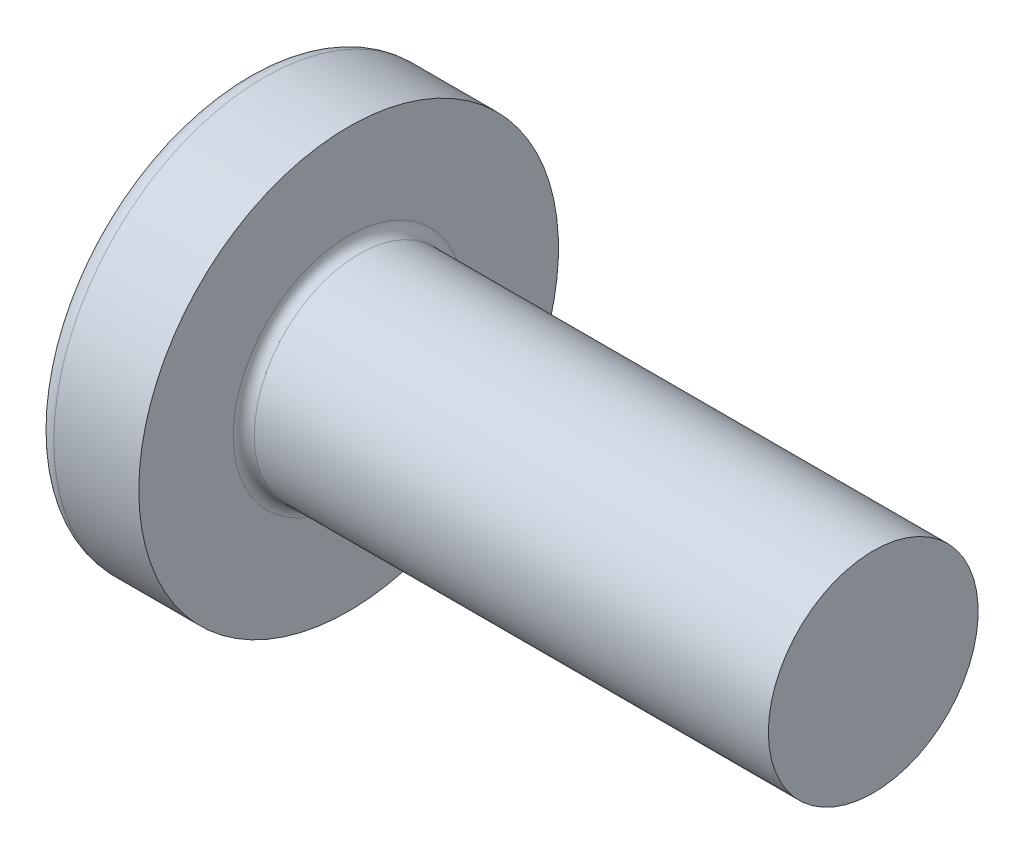
SolidWorks part; units mm, degrees
material "2018 合金"
ref_plane "Plane1" through (0, 0, 0) normal (0, 0, 1) x (1, 0, 0)
ref_plane "Plane2" through (0, 0, 0) normal (0, 1, 0) x (1, 0, 0)
ref_plane "Plane3" through (0, 0, 0) normal (1, 0, 0) x (0, 0, -1)
sketch "BodySke" plane through (0, 0, 0) normal (0, 0, 1) x (1, 0, 0)
  line L0 (1.6, 1) -> (1.6, 2)
  line L1 (1.8, 6.35) -> (1.8, -3.175) construction
  line L2 (-25.4, 0) -> (127, 0) construction
  line L3 (6.6, 0) -> (0, 0)
  line L4 (1.6, 1) -> (6.6, 1)
  line L5 (6.6, 1) -> (6.6, 0)
  line L6 (0.79, 2) -> (1.6, 2)
  line L8 (1.6, 6.35) -> (1.6, -3.175) construction
  arc A0 (0.6464, 1.9285) -> (0, 0) centre (3.2, 0) ccw
  arc A2 (0.6464, 1.9285) -> (0.79, 2) centre (0.79, 1.82) cw
  dimension "Head_crown_rad" = 3.2
  dimension "Head_fillet_rad" = 0.18
  dimension "Length" = 5
  dimension "Head_ht" = 1.6
  dimension "Head_dia" = 4
  dimension "Advance" = 0.4
  dimension "Thread_nom" = 5
  dimension "Diameter" = 2
revolve "Base-Revolve" add sketch "BodySke"
cosmetic thread "ThreadCosmetic" [suppressed]
fillet "Fillet1" radius 0.1 1 edges at (1.6, 0, 1)
sketch "Sketch3" plane through (0, 0, 0) normal (1, 0, 0) x (0, 0, -1)
  line L0 (0.24, -1.05) -> (-0.24, -1.05)
  line L1 (0.24, -1.05) -> (0.24, 1.05)
  line L2 (-0.24, 1.05) -> (0.24, 1.05)
  line L3 (-0.24, 1.05) -> (-0.24, -1.05)
  dimension "Cross_dia" = 2.1
  dimension "D1" = 1.05
  dimension "Cross_width" = 0.48
  dimension "D2" = 0.24
ref_plane "Plane4" through (1.42, 0, 0) normal (1, 0, 0) x (0, 0, -1)
sketch "Sketch4" plane through (1.42, 0, 0) normal (1, 0, 0) x (0, 0, -1)
  line L0 (0.24, -0.342) -> (-0.24, -0.342)
  line L1 (0.24, -0.342) -> (0.24, 0.342)
  line L2 (-0.24, 0.342) -> (0.24, 0.342)
  line L3 (-0.24, 0.342) -> (-0.24, -0.342)
  dimension "D1" = 0.48
  dimension "D2" = 0.684
  dimension "D3" = 0.24
  dimension "D4" = 0.342
loft "Recess" cut profiles "Sketch3", "Sketch4"
pattern_circular "RecPat" count 2 every 90 about axis through (0, 0, 0) along (1, 0, 0) of "Recess"
sketch "RecCorSke" plane through (0, 0, 0) normal (0, 0, 1) x (1, 0, 0)
  line L0 (-3.175, 0) -> (15.875, 0) construction
  line L1 (-25.4, 0) -> (127, 0) construction
  line L2 (0, 0) -> (0, 0.4548)
  line L3 (0, 0.4548) -> (1.42, 0.3555)
  line L4 (1.42, 0.3555) -> (1.5355, 0)
  line L5 (1.5355, 0) -> (0, 0)
  dimension "Diameter" = 0.711
  dimension "Depth" = 1.42
  dimension "Draft_angle" = 4
  dimension "Bottom_angle" = 18
revolve "RecessCore" cut sketch "RecCorSke" angle 360 about L0
sketch "ThdSchSke" plane through (0, 0, 0) normal (0, 0, 1) x (1, 0, 0)
  line L0 (2.4, -0.774) -> (2.2418, -1)
  line L1 (2.4, -0.774) -> (2.5582, -1)
  line L2 (2.5582, -1) -> (2.5582, -1.25)
  line L3 (-3.175, 0) -> (5.1513, 0) construction
  line L5 (2.5582, -1.25) -> (2.2418, -1.25)
  line L6 (2.2418, -1.25) -> (2.2418, -1)
  dimension "Diameter" = 2
  dimension "SideAngle" = 55
  dimension "VeeAngle" = 70
  dimension "Thread_minor" = 1.548
  dimension "Overcut" = 2.5
  dimension "Start" = 2.4
revolve "ThreadSchematic" [suppressed] cut sketch "ThdSchSke" angle 360 about L3
pattern_linear "ThdSchPat" [suppressed]
equation "\"D1@Sketch3\" = \"Cross_dia@Sketch3\" / 2"
equation "\"D2@Sketch3\" = \"Cross_width@Sketch3\" / 2"
equation "\"Depth@RecCorSke\" = \"Cross_depth@Plane4\""
equation "\"D1@Sketch4\" = \"Cross_width@Sketch3\""
equation "\"D2@Sketch4\" = \"Cross_dia@Sketch3\" - 2.0 * \"Cross_depth@Plane4\" * tan(26.5  * 0.017453292)"
equation "\"D3@Sketch4\" = \"D1@Sketch4\" / 2"
equation "\"D4@Sketch4\" = \"D2@Sketch4\" / 2"
equation "\"Thread_length@ThreadCosmetic\" = ((sgn( (\"Length@BodySke\" - \"Advance@BodySke\" * 2.0 ) - \"Thread_nom@BodySke\" )-1)*( (\"Length@BodySke\" - \"Advance@BodySke\" * 2.0 ) - \"Thread_nom@BodySke\" ))/-2+ \"Thread_nom@BodySke\""
equation "\"Thread_minor@ThdSchSke\" = \"Thread_minor@ThreadCosmetic\""
equation "\"Diameter@ThdSchSke\" = \"Diameter@BodySke\""
equation "\"Overcut@ThdSchSke\" = \"Diameter@BodySke\" * 1.25"
equation "\"Start@ThdSchSke\" = \"Head_ht@BodySke\" + \"Length@BodySke\" - \"Thread_length@ThreadCosmetic\"  '---Non-countersunk---"
equation "\"Num_threads@ThdSchPat\" = int( \"Thread_length@ThreadCosmetic\" / \"Advance@BodySke\" + 0.999 )  + 1"
equation "\"Advance@ThdSchPat\" = \"Thread_length@ThreadCosmetic\" /  (\"Num_threads@ThdSchPat\" - 1) 'relax it"
